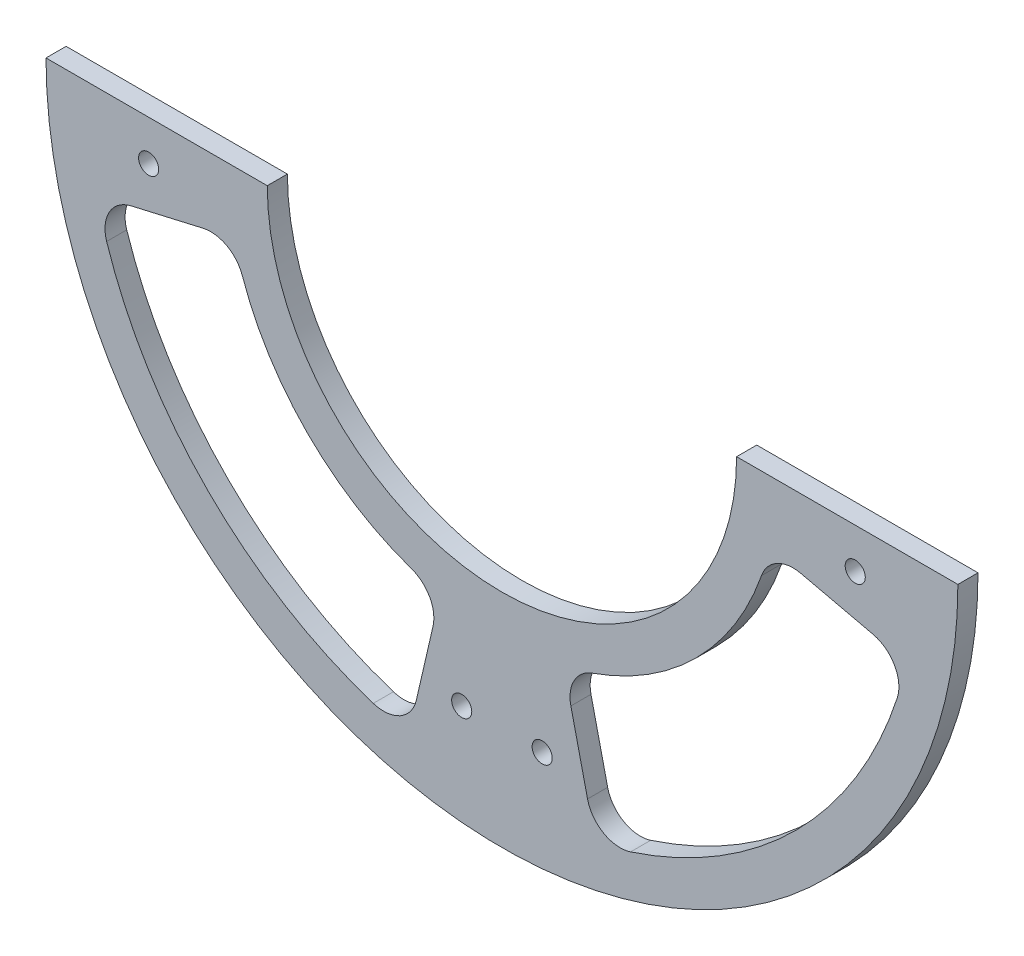
SolidWorks part; units mm, degrees
ref_plane "前视基准面" through (0, 0, 0) normal (0, 0, 1) x (1, 0, 0)
ref_plane "上视基准面" through (0, 0, 0) normal (0, 1, 0) x (1, 0, 0)
ref_plane "右视基准面" through (0, 0, 0) normal (1, 0, 0) x (0, 0, -1)
sketch "草图1" plane through (0, 0, 0) normal (0, 0, 1) x (1, 0, 0)
  line L0 (-66.8986, 2.6534) -> (-33.8986, 2.6534)
  line L1 (1.1014, 2.6534) -> (1.1014, -65.3466) construction
  line L2 (36.1014, 2.6534) -> (69.1014, 2.6534)
  arc A0 (-66.8986, 2.6534) -> (69.1014, 2.6534) centre (1.1014, 2.6534) ccw
  arc A1 (-33.8986, 2.6534) -> (36.1014, 2.6534) centre (1.1014, 2.6534) ccw
  circle A2 centre (-51.5881, -3.3466) radius 1.5
  circle A3 centre (-4.8986, -50.0361) radius 1.5
  circle A4 centre (7.1014, -50.0361) radius 1.5
  circle A5 centre (53.7909, -3.3466) radius 1.5
  circle A6 centre (1.1014, 2.6534) radius 53.03 construction
  dimension "D1" = 136
  dimension "D2" = 70
  dimension "D3" = 6
  dimension "D4" = 6
  dimension "D5" = 6
  dimension "D6" = 6
  dimension "D7" = 3
  dimension "D8" = 3
  dimension "D9" = 3
  dimension "D10" = 3
  dimension "D11" = 53.03
  dimension "D12" = 53.03
  dimension "D14" = 53.03
  dimension "D13" = 53.03
extrude "凸台-拉伸1" add sketch "草图1" along normal blind 3
sketch "草图2" plane through (0, 0, 3) normal (0, 0, 1) x (1, 0, 0)
  line L0 (10.3196, -37.2969) -> (15.0411, -57.7592)
  line L1 (41.0517, -6.5648) -> (61.514, -11.2863)
  line L2 (-8.1168, -37.2969) -> (-12.8383, -57.7592)
  line L3 (-38.8489, -6.5648) -> (-59.3112, -11.2863)
  arc A0 (-38.8489, -6.5648) -> (-8.1168, -37.2969) centre (1.1014, 2.6534) ccw
  arc A1 (-59.3112, -11.2863) -> (-12.8383, -57.7592) centre (1.1014, 2.6534) ccw
  arc A2 (-33.8986, 2.6534) -> (36.1014, 2.6534) centre (1.1014, 2.6534) ccw construction
  arc A3 (-66.8986, 2.6534) -> (69.1014, 2.6534) centre (1.1014, 2.6534) ccw construction
  circle A4 centre (-51.5881, -3.3466) radius 1.5 construction
  circle A5 centre (-4.8986, -50.0361) radius 1.5 construction
  circle A6 centre (7.1014, -50.0361) radius 1.5 construction
  circle A7 centre (53.7909, -3.3466) radius 1.5 construction
  arc A8 (10.3196, -37.2969) -> (41.0517, -6.5648) centre (1.1014, 2.6534) ccw
  arc A9 (15.0411, -57.7592) -> (61.514, -11.2863) centre (1.1014, 2.6534) ccw
  dimension "D1" = 6
  dimension "D2" = 6
  dimension "D3" = 6
  dimension "D4" = 6
  dimension "D5" = 6
  dimension "D6" = 6
extrude "切除-拉伸1" cut sketch "草图2" against normal blind 3
fillet "圆角1" radius 5 8 edges at (41.0517, -6.5648, 1.5) (61.514, -11.2863, 1.5) (15.0411, -57.7592, 1.5) (10.3196, -37.2969, 1.5) (-12.8383, -57.7592, 1.5) (-8.1168, -37.2969, 1.5) (-59.3112, -11.2863, 1.5) (-38.8489, -6.5648, 1.5)
